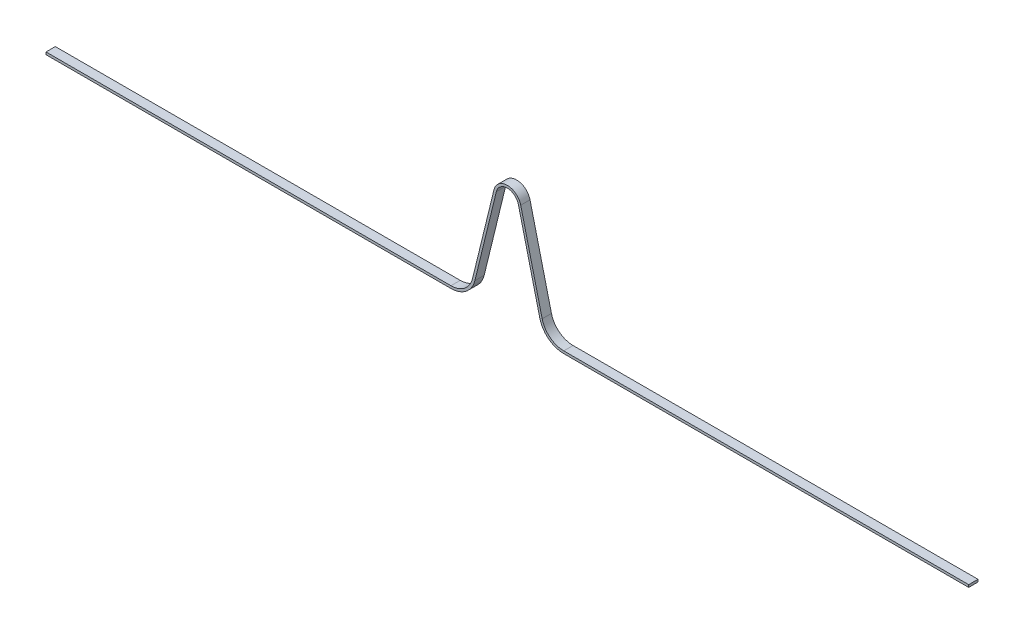
SolidWorks part; units mm, degrees
material "Rubber"
ref_plane "Front Plane" through (0, 0, 0) normal (0, 0, 1) x (1, 0, 0)
ref_plane "Top Plane" through (0, 0, 0) normal (0, 1, 0) x (1, 0, 0)
ref_plane "Right Plane" through (0, 0, 0) normal (1, 0, 0) x (0, 0, -1)
sketch "Sketch1" plane through (0, 0, 0) normal (0, 0, 1) x (1, 0, 0)
  line L0 (0, 0) -> (0, -42.55) construction
  line L1 (0, -42.55) -> (-30.32, -42.55) construction
  line L2 (-248, -54.5) -> (-30.32, -54.5)
  line L3 (-18.7117, -45.3874) -> (-7.1884, 1.757)
  line L4 (248, -54.5) -> (30.32, -54.5)
  line L5 (18.7117, -45.3874) -> (7.1884, 1.757)
  arc A0 (7.1884, 1.757) -> (-7.1884, 1.757) centre (0, 0) ccw
  arc A1 (-30.32, -54.5) -> (-18.7117, -45.3874) centre (-30.32, -42.55) ccw
  arc A2 (30.32, -54.5) -> (18.7117, -45.3874) centre (30.32, -42.55) cw
  dimension "D3" = 23.9
  dimension "D4" = 14.8
  dimension "D1" = 42.55
  dimension "D2" = 30.32
  dimension "D5" = 248
  dimension "D6" = 248
extrude "Extrude-Thin1" add sketch "Sketch1" along normal mid plane 5 thin
